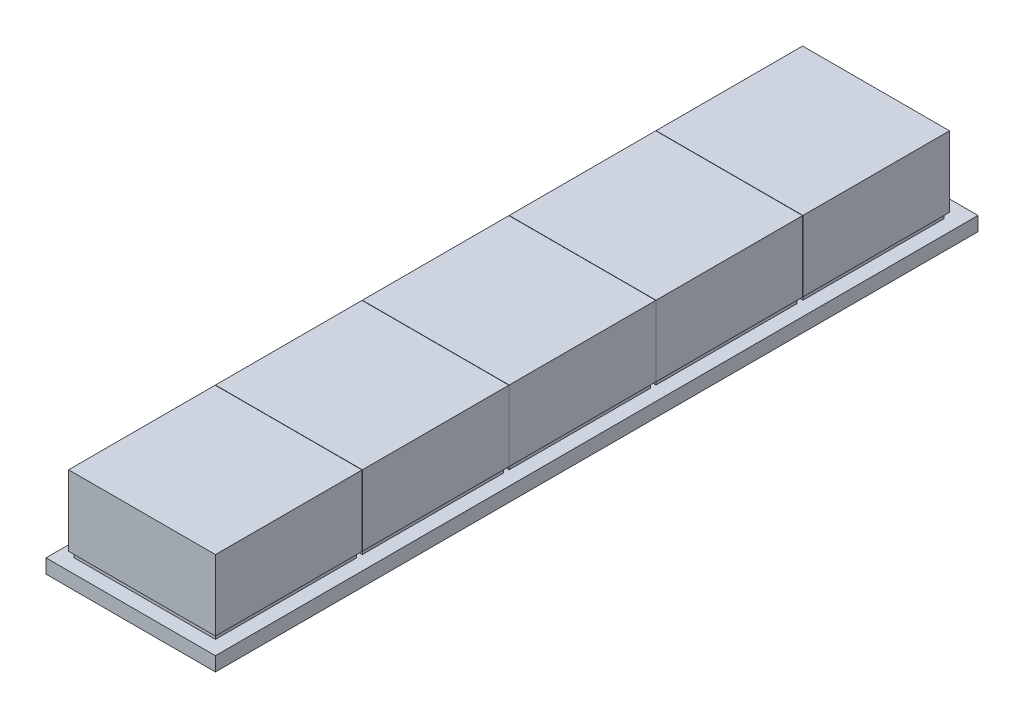
SolidWorks part; units mm, degrees
ref_plane "Front Plane" through (0, 0, 0) normal (0, 0, 1) x (1, 0, 0)
ref_plane "Top Plane" through (0, 0, 0) normal (0, 1, 0) x (1, 0, 0)
ref_plane "Right Plane" through (0, 0, 0) normal (1, 0, 0) x (0, 0, -1)
sketch "Sketch1" plane through (0, 0, 0) normal (0, 1, 0) x (1, 0, 0)
  line L1 (-30, -135) -> (30, -135)
  line L2 (-30, -135) -> (-30, 135)
  line L3 (-30, 135) -> (30, 135)
  line L4 (30, -135) -> (30, 135)
  line L5 (-30, -135) -> (30, 135) construction
  line L6 (-30, 135) -> (30, -135) construction
  point P0 (0, 0)
  dimension "D1" = 60
  dimension "D2" = 270
extrude "Boss-Extrude1" add sketch "Sketch1" along normal blind 5
sketch "Sketch2" plane through (0, 5, 0) normal (0, 1, 0) x (1, 0, 0)
  line L0 (0, 0) -> (0, -135) construction
  line L1 (-30, -135) -> (30, -135) construction
  line L3 (-25, -80) -> (25, -80)
  line L4 (-25, -80) -> (-25, -130)
  line L5 (-25, -130) -> (25, -130)
  line L6 (25, -80) -> (25, -130)
  line L7 (-25, -80) -> (25, -130) construction
  line L8 (-25, -130) -> (25, -80) construction
  point P5 (0, -105)
  dimension "D1" = 50
  dimension "D2" = 50
  dimension "D3" = 5
extrude "Boss-Extrude3" add sketch "Sketch2" along normal blind 2
pattern_linear "LPattern1" count 5 spacing 52 along (0, 0, -1) of "Boss-Extrude3"
sketch "Sketch3" plane through (0, 7, 0) normal (0, 1, 0) x (1, 0, 0)
  line L0 (0, 0) -> (0, -130) construction
  line L1 (-25, -130) -> (25, -130) construction
  line L3 (-26, -79.1) -> (26, -79.1)
  line L4 (-26, -79.1) -> (-26, -131)
  line L5 (-26, -131) -> (26, -131)
  line L6 (26, -79.1) -> (26, -131)
  line L7 (-26, -79.1) -> (26, -131) construction
  line L8 (-26, -131) -> (26, -79.1) construction
  line L9 (-30, -135) -> (30, -135) construction
  point P5 (0, -105.05)
  dimension "D1" = 52
  dimension "D2" = 51.9
  dimension "D3" = 4
extrude "Boss-Extrude8" add sketch "Sketch3" along normal blind 25
pattern_linear "LPattern5" count 5 spacing 52 along (0, 0, -1) of "Boss-Extrude8"
